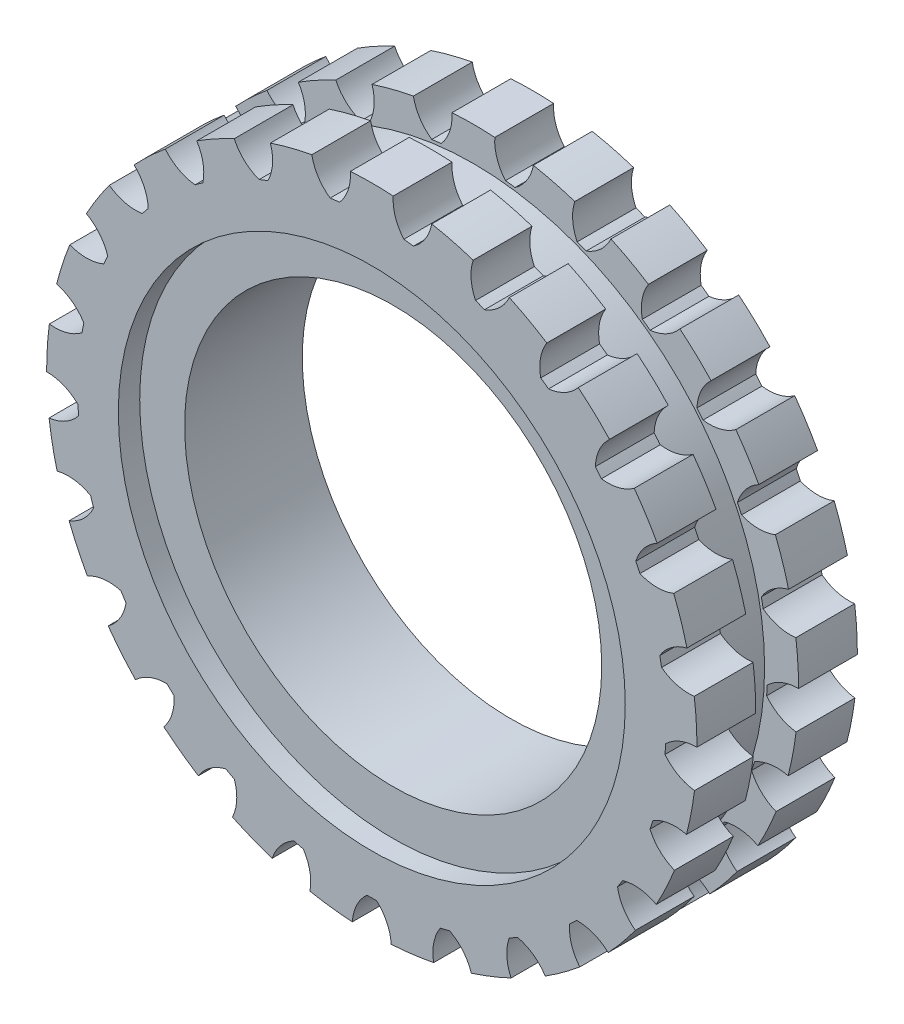
SolidWorks part; units mm, degrees
ref_plane "Ebene vorne" through (0, 0, 0) normal (0, 0, 1) x (1, 0, 0)
ref_plane "Ebene oben" through (0, 0, 0) normal (0, 1, 0) x (1, 0, 0)
ref_plane "Ebene rechts" through (0, 0, 0) normal (1, 0, 0) x (0, 0, -1)
sketch "Skizze1" plane through (0, 0, 0) normal (1, 0, 0) x (0, 0, -1)
  line L0 (-5.5, 0) -> (5.5, 0)
  line L1 (-17.3304, -19.5) -> (23.4195, -19.5) construction
  line L2 (0, 0) -> (0, 8) construction
  line L3 (-5.5, 0) -> (-5.5, 4.2)
  line L4 (-5.5, 4.2) -> (-7.5, 4.2)
  line L5 (-7.5, 4.2) -> (-7.5, 8)
  line L6 (-7.5, 8) -> (7.5, 8)
  line L7 (7.5, 4.2) -> (7.5, 8)
  line L8 (5.5, 4.2) -> (7.5, 4.2)
  line L9 (5.5, 0) -> (5.5, 4.2)
  dimension "D1" = 8
  dimension "D2" = 3.8
  dimension "D3" = 11
  dimension "D4" = 2
  dimension "D5" = 55
revolve "Rotation1" add sketch "Skizze1" angle 360 about L1
sketch "Skizze2" plane through (0, 0, 7.5) normal (0, 0, 1) x (1, 0, 0)
  line L1 (0, 18.2198) -> (0, 8) construction
  line L2 (0, 8) -> (0, -19.5) construction
  line L3 (-2, 10.8359) -> (-3.0133, 26.2056) construction
  line L5 (-14.952, 9.982) -> (-2, 10.8359) construction
  circle A1 centre (0, -19.5) radius 27.5 construction
  arc A76 (-3, 7.8359) -> (3, 7.8359) centre (0, -19.5) cw
  arc A77 (-3, 7.8359) -> (-2, 10.8359) centre (-6.1744, 10.5607) ccw
  arc A78 (-2, 10.8359) -> (2, 10.8359) centre (0, -19.5) cw
  arc A79 (3, 7.8359) -> (2, 10.8359) centre (6.1744, 10.5607) cw
  arc A80 (5.6071, 10.3802) -> (9.4814, 9.3854) centre (0, -19.5) cw
  arc A81 (3.8924, 7.7231) -> (5.6071, 10.3802) centre (1.4954, 11.1518) ccw
  arc A82 (3.8924, 7.7231) -> (9.7039, 6.231) centre (0, -19.5) cw
  arc A83 (9.7039, 6.231) -> (9.4814, 9.3854) centre (13.4562, 8.0807) cw
  arc A84 (12.8618, 8.047) -> (16.367, 6.12) centre (0, -19.5) cw
  arc A85 (10.5402, 5.8999) -> (12.8618, 8.047) centre (9.0712, 9.8169) ccw
  arc A86 (10.5402, 5.8999) -> (15.7981, 3.0093) centre (0, -19.5) cw
  arc A87 (15.7981, 3.0093) -> (16.367, 6.12) centre (19.8925, 3.8678) cw
  arc A88 (19.3084, 3.983) -> (22.2243, 1.2448) centre (0, -19.5) cw
  arc A89 (16.5258, 2.4806) -> (19.3084, 3.983) centre (16.077, 6.6399) ccw
  arc A90 (16.5258, 2.4806) -> (20.8996, -1.6266) centre (0, -19.5) cw
  arc A91 (20.8996, -1.6266) -> (22.2243, 1.2448) centre (25.0789, -1.8134) cw
  arc A92 (24.5418, -1.5566) -> (26.6851, -4.9339) centre (0, -19.5) cw
  arc A93 (21.473, -2.3197) -> (24.5418, -1.5566) centre (22.0727, 1.8205) ccw
  arc A94 (21.473, -2.3197) -> (24.6879, -7.3857) centre (0, -19.5) cw
  arc A95 (24.6879, -7.3857) -> (26.6851, -4.9339) centre (28.6895, -8.6059) cw
  arc A96 (28.2331, -8.2236) -> (29.4692, -12.0278) centre (0, -19.5) cw
  arc A97 (25.0709, -8.1996) -> (28.2331, -8.2236) centre (26.6814, -4.3386) ccw
  arc A98 (25.0709, -8.1996) -> (26.925, -13.9059) centre (0, -19.5) cw
  arc A99 (26.925, -13.9059) -> (29.4692, -12.0278) centre (30.4974, -16.0829) cw
  arc A100 (30.1504, -15.5991) -> (30.4016, -19.5912) centre (0, -19.5) cw
  arc A101 (27.0936, -14.7895) -> (30.1504, -15.5991) centre (29.6137, -11.4503) ccw
  arc A102 (27.0936, -14.7895) -> (27.4703, -20.7776) centre (0, -19.5) cw
  arc A103 (27.4703, -20.7776) -> (30.4016, -19.5912) centre (30.389, -23.7747) cw
  arc A104 (30.1733, -23.2198) -> (29.4238, -27.149) centre (0, -19.5) cw
  arc A105 (27.4138, -21.6754) -> (30.1733, -23.2198) centre (30.6852, -19.0678) ccw
  arc A106 (27.4138, -21.6754) -> (26.2895, -27.5691) centre (0, -19.5) cw
  arc A107 (26.2895, -27.5691) -> (29.4238, -27.149) centre (28.3712, -31.1978) cw
  arc A108 (28.3003, -30.6067) -> (26.5972, -34.226) centre (0, -19.5) cw
  arc A109 (26.0116, -28.4246) -> (28.3003, -30.6067) centre (29.8286, -26.7125) ccw
  arc A110 (26.0116, -28.4246) -> (23.4569, -33.8535) centre (0, -19.5) cw
  arc A111 (23.4569, -33.8535) -> (26.5972, -34.226) centre (24.5708, -37.8859) cw
  arc A112 (24.649, -37.2958) -> (22.0993, -40.3778) centre (0, -19.5) cw
  arc A113 (22.9749, -34.613) -> (24.649, -37.2958) centre (27.0978, -33.904) ccw
  arc A114 (22.9749, -34.613) -> (19.1504, -39.2361) centre (0, -19.5) cw
  arc A115 (19.1504, -39.2361) -> (22.0993, -40.3778) centre (19.2264, -43.4188) cw
  arc A116 (19.449, -42.8667) -> (16.2129, -45.2178) centre (0, -19.5) cw
  arc A117 (18.4947, -39.8518) -> (19.449, -42.8667) centre (22.6644, -40.1904) ccw
  arc A118 (18.4947, -39.8518) -> (13.6406, -43.3785) centre (0, -19.5) cw
  arc A119 (13.6406, -43.3785) -> (16.2129, -45.2178) centre (12.674, -47.4488) cw
  arc A120 (13.0269, -46.9693) -> (9.3078, -48.4418) centre (0, -19.5) cw
  arc A121 (12.8523, -43.8119) -> (13.0269, -46.9693) centre (16.8069, -45.1768) ccw
  arc A122 (12.8523, -43.8119) -> (7.2737, -46.0206) centre (0, -19.5) cw
  arc A123 (7.2737, -46.0206) -> (9.3078, -48.4418) centre (5.3253, -49.7226) cw
  arc A124 (5.7863, -49.346) -> (1.8179, -49.8473) centre (0, -19.5) cw
  arc A125 (6.4024, -46.2443) -> (5.7863, -49.346) centre (9.8933, -48.5498) ccw
  arc A126 (6.4024, -46.2443) -> (0.4497, -46.9963) centre (0, -19.5) cw
  arc A127 (0.4497, -46.9963) -> (1.8179, -49.8473) centre (-2.3581, -50.0975) cw
  arc A128 (-1.8179, -49.8473) -> (-5.7863, -49.346) centre (0, -19.5) cw
  arc A129 (-0.4497, -46.9963) -> (-1.8179, -49.8473) centre (2.3581, -50.0975) ccw
  arc A130 (-0.4497, -46.9963) -> (-6.4024, -46.2443) centre (0, -19.5) cw
  arc A131 (-6.4024, -46.2443) -> (-5.7863, -49.346) centre (-9.8933, -48.5498) cw
  arc A132 (-9.3078, -48.4418) -> (-13.0269, -46.9693) centre (0, -19.5) cw
  arc A133 (-7.2737, -46.0206) -> (-9.3078, -48.4418) centre (-5.3253, -49.7226) ccw
  arc A134 (-7.2737, -46.0206) -> (-12.8523, -43.8119) centre (0, -19.5) cw
  arc A135 (-12.8523, -43.8119) -> (-13.0269, -46.9693) centre (-16.8069, -45.1768) cw
  arc A136 (-16.2129, -45.2178) -> (-19.449, -42.8667) centre (0, -19.5) cw
  arc A137 (-13.6406, -43.3785) -> (-16.2129, -45.2178) centre (-12.674, -47.4488) ccw
  arc A138 (-13.6406, -43.3785) -> (-18.4947, -39.8518) centre (0, -19.5) cw
  arc A139 (-18.4947, -39.8518) -> (-19.449, -42.8667) centre (-22.6644, -40.1904) cw
  arc A140 (-22.0993, -40.3778) -> (-24.649, -37.2958) centre (0, -19.5) cw
  arc A141 (-19.1504, -39.2361) -> (-22.0993, -40.3778) centre (-19.2264, -43.4188) ccw
  arc A142 (-19.1504, -39.2361) -> (-22.9749, -34.613) centre (0, -19.5) cw
  arc A143 (-22.9749, -34.613) -> (-24.649, -37.2958) centre (-27.0978, -33.904) cw
  arc A144 (-26.5972, -34.226) -> (-28.3003, -30.6067) centre (0, -19.5) cw
  arc A145 (-23.4569, -33.8535) -> (-26.5972, -34.226) centre (-24.5708, -37.8859) ccw
  arc A146 (-23.4569, -33.8535) -> (-26.0116, -28.4246) centre (0, -19.5) cw
  arc A147 (-26.0116, -28.4246) -> (-28.3003, -30.6067) centre (-29.8286, -26.7125) cw
  arc A148 (-29.4238, -27.149) -> (-30.1733, -23.2198) centre (0, -19.5) cw
  arc A149 (-26.2895, -27.5691) -> (-29.4238, -27.149) centre (-28.3712, -31.1978) ccw
  arc A150 (-26.2895, -27.5691) -> (-27.4138, -21.6754) centre (0, -19.5) cw
  arc A151 (-27.4138, -21.6754) -> (-30.1733, -23.2198) centre (-30.6852, -19.0678) cw
  arc A152 (-30.4016, -19.5912) -> (-30.1504, -15.5991) centre (0, -19.5) cw
  arc A153 (-27.4703, -20.7776) -> (-30.4016, -19.5912) centre (-30.389, -23.7747) ccw
  arc A154 (-27.4703, -20.7776) -> (-27.0936, -14.7895) centre (0, -19.5) cw
  arc A155 (-27.0936, -14.7895) -> (-30.1504, -15.5991) centre (-29.6137, -11.4503) cw
  arc A156 (-29.4692, -12.0278) -> (-28.2331, -8.2236) centre (0, -19.5) cw
  arc A157 (-26.925, -13.9059) -> (-29.4692, -12.0278) centre (-30.4974, -16.0829) ccw
  arc A158 (-26.925, -13.9059) -> (-25.0709, -8.1996) centre (0, -19.5) cw
  arc A159 (-25.0709, -8.1996) -> (-28.2331, -8.2236) centre (-26.6814, -4.3386) cw
  arc A160 (-26.6851, -4.9339) -> (-24.5418, -1.5566) centre (0, -19.5) cw
  arc A161 (-24.6879, -7.3857) -> (-26.6851, -4.9339) centre (-28.6895, -8.6059) ccw
  arc A162 (-24.6879, -7.3857) -> (-21.473, -2.3197) centre (0, -19.5) cw
  arc A163 (-21.473, -2.3197) -> (-24.5418, -1.5566) centre (-22.0727, 1.8205) cw
  arc A164 (-22.2243, 1.2448) -> (-19.3084, 3.983) centre (0, -19.5) cw
  arc A165 (-20.8996, -1.6266) -> (-22.2243, 1.2448) centre (-25.0789, -1.8134) ccw
  arc A166 (-20.8996, -1.6266) -> (-16.5258, 2.4806) centre (0, -19.5) cw
  arc A167 (-16.5258, 2.4806) -> (-19.3084, 3.983) centre (-16.077, 6.6399) cw
  arc A168 (-16.367, 6.12) -> (-12.8618, 8.047) centre (0, -19.5) cw
  arc A169 (-15.7981, 3.0093) -> (-16.367, 6.12) centre (-19.8925, 3.8678) ccw
  arc A170 (-15.7981, 3.0093) -> (-10.5402, 5.8999) centre (0, -19.5) cw
  arc A171 (-10.5402, 5.8999) -> (-12.8618, 8.047) centre (-9.0712, 9.8169) cw
  arc A172 (-9.4814, 9.3854) -> (-5.6071, 10.3802) centre (0, -19.5) cw
  arc A173 (-9.7039, 6.231) -> (-9.4814, 9.3854) centre (-13.4562, 8.0807) ccw
  arc A174 (-9.7039, 6.231) -> (-3.8924, 7.7231) centre (0, -19.5) cw
  arc A175 (-3.8924, 7.7231) -> (-5.6071, 10.3802) centre (-1.4954, 11.1518) cw
  point P160 (0, -19.5)
  dimension "D3" = 3
  dimension "D1" = 6
  dimension "D2" = 4
extrude "Aufsatz-Linear austragen1" add sketch "Skizze2" against normal through all
sketch "Skizze3" plane through (0, 0, 0) normal (1, 0, 0) x (0, 0, -1)
  line L0 (0, 7.7231) -> (0, 0) construction
  line L1 (-2, 11.3359) -> (2, 11.3359)
  line L2 (-2, 11.3359) -> (-2, 7.7231)
  line L3 (-2, 7.7231) -> (2, 7.7231)
  line L4 (2, 11.3359) -> (2, 7.7231)
  line L6 (7.5, 10.8359) -> (-7.5, 10.8359) construction
  line L7 (-15.257, -19.5057) -> (27.6114, -19.5057) construction
  line L8 (-15.257, 10.8359) -> (-15.257, -49.8473) construction
  line L9 (-15.257, -49.8473) -> (-7.5, -49.8473) construction
  line L10 (-15.257, 10.8359) -> (-7.5, 10.8359) construction
  line L12 (7.5, 7.7231) -> (-7.5, 7.7231) construction
  dimension "D1" = 4
  dimension "D2" = 0.5
revolve "Schnitt-Rotation2" cut sketch "Skizze3" angle 360 about L7
